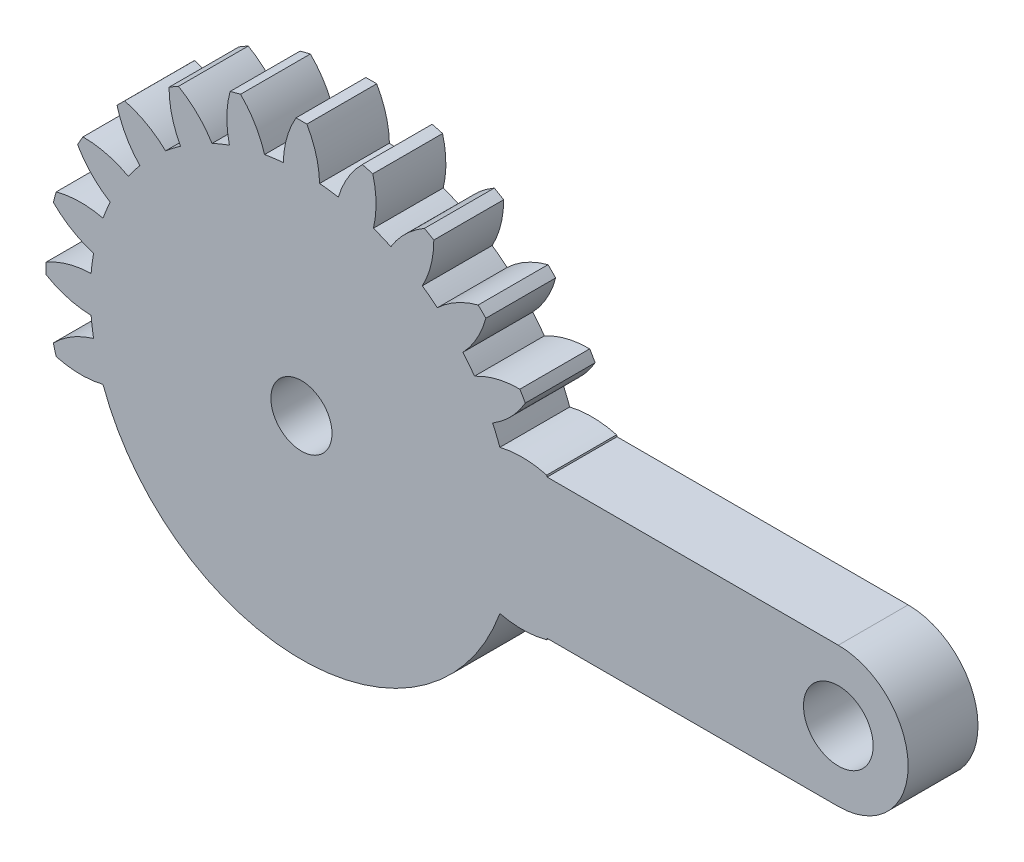
SolidWorks part; units mm, degrees
ref_plane "Front Plane" through (0, 0, 0) normal (0, 0, 1) x (1, 0, 0)
ref_plane "Top Plane" through (0, 0, 0) normal (0, 1, 0) x (1, 0, 0)
ref_plane "Right Plane" through (0, 0, 0) normal (1, 0, 0) x (0, 0, -1)
sketch "Sketch1" plane through (0, 0, 0) normal (0, 0, 1) x (1, 0, 0)
  point P158 (0, 0)
  point P159 (0, 0)
sketch "Sketch2" plane through (0, 0, 0) normal (0, 0, 1) x (1, 0, 0)
  line L0 (0, 0) -> (0, 14630) construction
  line L1 (0, 0) -> (48123.3485, 0) construction
  line L2 (11409.1235, 4000) -> (30750, 4000)
  line L3 (30750, -4000) -> (11409.1235, -4000)
  circle A0 centre (0, 0) radius 1750
  circle A1 centre (0, 0) radius 12090
  circle A2 centre (0, 0) radius 14630
  arc A3 (310, 14626.7153) -> (1040, 12045.1858) centre (-4358.3726, 11912.623) cw
  arc A4 (-310, 14626.7153) -> (-1040, 12045.1858) centre (4358.3726, 11912.623) ccw
  arc A5 (4085.1095, 14048.0881) -> (4122.0863, 11365.5842) centre (-1126.651, 12634.7401) cw
  arc A6 (3486.2355, 14208.556) -> (2112.9606, 11903.9278) centre (7293.0784, 10378.6804) ccw
  arc A7 (7581.8255, 12512.107) -> (6923.2593, 9911.4369) centre (2181.8501, 12495.8205) cw
  arc A8 (7044.8898, 12822.107) -> (5121.9265, 10951.4369) centre (9730.7729, 8137.4478) ccw
  arc A9 (10561.8527, 10123.4465) -> (9252.6236, 7781.8415) centre (5341.6617, 11505.3313) cw
  arc A10 (10123.4465, 10561.8527) -> (7781.8415, 9252.6236) centre (11505.3313, 5341.6617) ccw
  arc A11 (12822.107, 7044.8898) -> (10951.4369, 5121.9265) centre (8137.4478, 9730.7729) cw
  arc A12 (12512.107, 7581.8255) -> (9911.4369, 6923.2593) centre (12495.8205, 2181.8501) ccw
  arc A13 (14208.556, 3486.2355) -> (11903.9278, 2112.9606) centre (10378.6804, 7293.0784) cw
  arc A14 (14048.0881, 4085.1095) -> (11365.5842, 4122.0863) centre (12634.7401, -1126.651) ccw
  arc A15 (14626.7153, -310) -> (12045.1858, -1040) centre (11912.623, 4358.3726) cw
  arc A16 (14626.7153, 310) -> (12045.1858, 1040) centre (11912.623, -4358.3726) ccw
  arc A17 (14048.0881, -4085.1095) -> (11365.5842, -4122.0863) centre (12634.7401, 1126.651) cw
  arc A18 (14208.556, -3486.2355) -> (11903.9278, -2112.9606) centre (10378.6804, -7293.0784) ccw
  arc A19 (12512.107, -7581.8255) -> (9911.4369, -6923.2593) centre (12495.8205, -2181.8501) cw
  arc A20 (12822.107, -7044.8898) -> (10951.4369, -5121.9265) centre (8137.4478, -9730.7729) ccw
  arc A21 (10123.4465, -10561.8527) -> (7781.8415, -9252.6236) centre (11505.3313, -5341.6617) cw
  arc A22 (10561.8527, -10123.4465) -> (9252.6236, -7781.8415) centre (5341.6617, -11505.3313) ccw
  arc A23 (7044.8898, -12822.107) -> (5121.9265, -10951.4369) centre (9730.7729, -8137.4478) cw
  arc A24 (7581.8255, -12512.107) -> (6923.2593, -9911.4369) centre (2181.8501, -12495.8205) ccw
  arc A25 (3486.2355, -14208.556) -> (2112.9606, -11903.9278) centre (7293.0784, -10378.6804) cw
  arc A26 (4085.1095, -14048.0881) -> (4122.0863, -11365.5842) centre (-1126.651, -12634.7401) ccw
  arc A27 (-310, -14626.7153) -> (-1040, -12045.1858) centre (4358.3726, -11912.623) cw
  arc A28 (310, -14626.7153) -> (1040, -12045.1858) centre (-4358.3726, -11912.623) ccw
  arc A29 (-4085.1095, -14048.0881) -> (-4122.0863, -11365.5842) centre (1126.651, -12634.7401) cw
  arc A30 (-3486.2355, -14208.556) -> (-2112.9606, -11903.9278) centre (-7293.0784, -10378.6804) ccw
  arc A31 (-7581.8255, -12512.107) -> (-6923.2593, -9911.4369) centre (-2181.8501, -12495.8205) cw
  arc A32 (-7044.8898, -12822.107) -> (-5121.9265, -10951.4369) centre (-9730.7729, -8137.4478) ccw
  arc A33 (-10561.8527, -10123.4465) -> (-9252.6236, -7781.8415) centre (-5341.6617, -11505.3313) cw
  arc A34 (-10123.4465, -10561.8527) -> (-7781.8415, -9252.6236) centre (-11505.3313, -5341.6617) ccw
  arc A35 (-12822.107, -7044.8898) -> (-10951.4369, -5121.9265) centre (-8137.4478, -9730.7729) cw
  arc A36 (-12512.107, -7581.8255) -> (-9911.4369, -6923.2593) centre (-12495.8205, -2181.8501) ccw
  arc A37 (-14208.556, -3486.2355) -> (-11903.9278, -2112.9606) centre (-10378.6804, -7293.0784) cw
  arc A38 (-14048.0881, -4085.1095) -> (-11365.5842, -4122.0863) centre (-12634.7401, 1126.651) ccw
  arc A39 (-14626.7153, 310) -> (-12045.1858, 1040) centre (-11912.623, -4358.3726) cw
  arc A40 (-14626.7153, -310) -> (-12045.1858, -1040) centre (-11912.623, 4358.3726) ccw
  arc A41 (-14048.0881, 4085.1095) -> (-11365.5842, 4122.0863) centre (-12634.7401, -1126.651) cw
  arc A42 (-14208.556, 3486.2355) -> (-11903.9278, 2112.9606) centre (-10378.6804, 7293.0784) ccw
  arc A43 (-12512.107, 7581.8255) -> (-9911.4369, 6923.2593) centre (-12495.8205, 2181.8501) cw
  arc A44 (-12822.107, 7044.8898) -> (-10951.4369, 5121.9265) centre (-8137.4478, 9730.7729) ccw
  arc A45 (-10123.4465, 10561.8527) -> (-7781.8415, 9252.6236) centre (-11505.3313, 5341.6617) cw
  arc A46 (-10561.8527, 10123.4465) -> (-9252.6236, 7781.8415) centre (-5341.6617, 11505.3313) ccw
  arc A47 (-7044.8898, 12822.107) -> (-5121.9265, 10951.4369) centre (-9730.7729, 8137.4478) cw
  arc A48 (-7581.8255, 12512.107) -> (-6923.2593, 9911.4369) centre (-2181.8501, 12495.8205) ccw
  arc A49 (-3486.2355, 14208.556) -> (-2112.9606, 11903.9278) centre (-7293.0784, 10378.6804) cw
  arc A50 (-4085.1095, 14048.0881) -> (-4122.0863, 11365.5842) centre (1126.651, 12634.7401) ccw
  arc A51 (30750, 4000) -> (30750, -4000) centre (30750, 0) cw
  circle A52 centre (30750, 0) radius 1995
  point P153 (0, 0)
  point P158 (8191.1017, 13609.0294)
  point P159 (6389.7689, 11829.834)
  point P160 (0, 0)
  point P161 (0, 0)
  point P162 (0, 0)
  point P163 (0, 0)
  point P164 (0, 0)
  point P165 (0, 0)
  point P166 (-21987.4233, 10011.5273)
  point P167 (-35629.0454, 9881.4529)
  dimension "D1" = 3500
  dimension "D2" = 24180
  dimension "D3" = 24180
  dimension "D4" = 29260
  dimension "D7" = 5400
  dimension "D9" = 4000
  dimension "D10" = 3990
  dimension "D5" = 620
  dimension "D6" = 2080
  dimension "D8" = 30750
  dimension "D11" = 24
extrude "Boss-Extrude1" add sketch "Sketch2" along normal blind 4000 contours A51 L2 A2 L3 A52 | A1 | A13 A2 L2 A1 | A2 A14 A1 L2 | A2 A16 A1 A15 | A16 A2 A13 A1 | A18 A2 A15 A1 | A2 A18 A1 L3 | A17 A2 L3 A1 | A2 A12 A1 A11 | A2 A10 A1 A9 | A2 A8 A1 A7 | A2 A6 A1 A5 | A2 A4 A1 A3 | A2 A50 A1 A49 | A2 A48 A1 A47 | A2 A46 A1 A45 | A2 A44 A1 A43 | A2 A42 A1 A41 | A2 A40 A1 A39 | A2 A38 A1 A37
